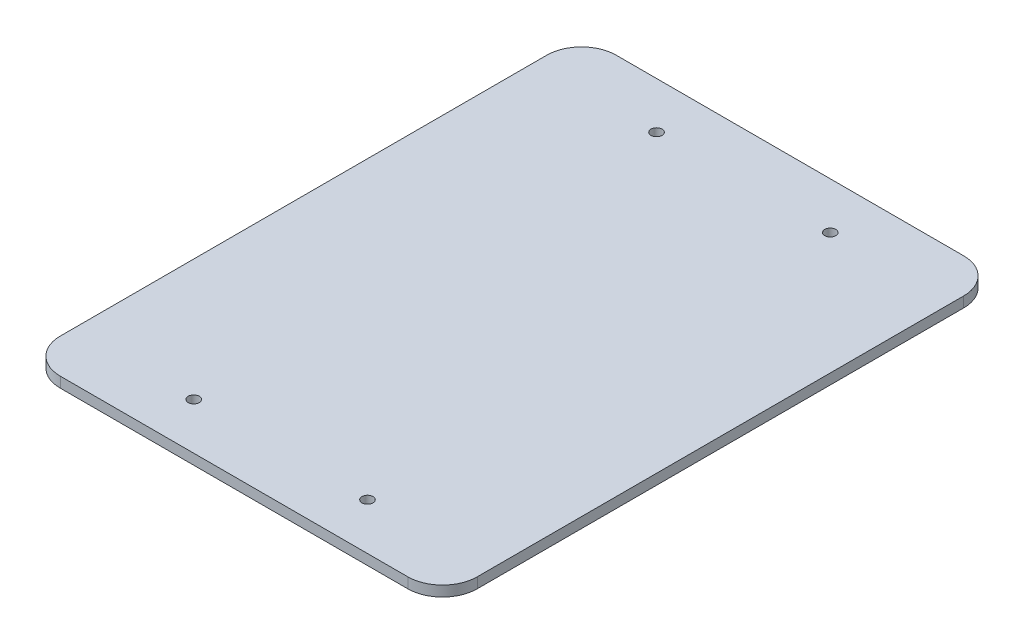
SolidWorks part; units mm, degrees
ref_plane "Alzado" through (0, 0, 0) normal (0, 0, 1) x (1, 0, 0)
ref_plane "Planta" through (0, 0, 0) normal (0, 1, 0) x (1, 0, 0)
ref_plane "Vista lateral" through (0, 0, 0) normal (1, 0, 0) x (0, 0, -1)
sketch "Croquis1" plane through (0, 0, 0) normal (0, 1, 0) x (1, 0, 0)
  line L1 (10, 0) -> (110, 0)
  line L2 (0, 10) -> (0, 150)
  line L3 (10, 160) -> (110, 160)
  line L4 (120, 10) -> (120, 150)
  arc A0 (110, 0) -> (120, 10) centre (110, 10) ccw
  arc A1 (10, 0) -> (0, 10) centre (10, 10) cw
  arc A2 (110, 160) -> (120, 150) centre (110, 150) cw
  arc A3 (0, 150) -> (10, 160) centre (10, 150) cw
  point P7 (120, 0)
  point P10 (0, 0)
  point P15 (0, 160)
  dimension "D3" = 10
  dimension "D1" = 160
  dimension "D2" = 120
extrude "Saliente-Extruir1" add sketch "Croquis1" along normal blind 3
sketch "Croquis2" plane through (0, 3, 0) normal (0, 1, 0) x (1, 0, 0)
  line L0 (35, 146.59) -> (85, 146.59) construction
  line L1 (35, 13.41) -> (85, 13.41) construction
  line L2 (110, 160) -> (10, 160) construction
  line L3 (10, 0) -> (110, 0) construction
  line L4 (60, 146.59) -> (60, 13.41) construction
  line L5 (120, 10) -> (120, 150) construction
  circle A0 centre (35, 146.59) radius 1.5875
  circle A1 centre (85, 146.59) radius 1.5875
  circle A2 centre (35, 13.41) radius 1.5875
  circle A3 centre (85, 13.41) radius 1.5875
  point P10 (60, 160)
  point P11 (60, 146.59)
  point P12 (60, 13.41)
  point P15 (60, 0)
  point P18 (60, 80)
  point P21 (120, 80)
  dimension "D1" = 3.175
  dimension "D2" = 50
  dimension "D3" = 50
  dimension "D4" = 133.18
extrude "Cortar-Extruir1" cut sketch "Croquis2" against normal blind 10
